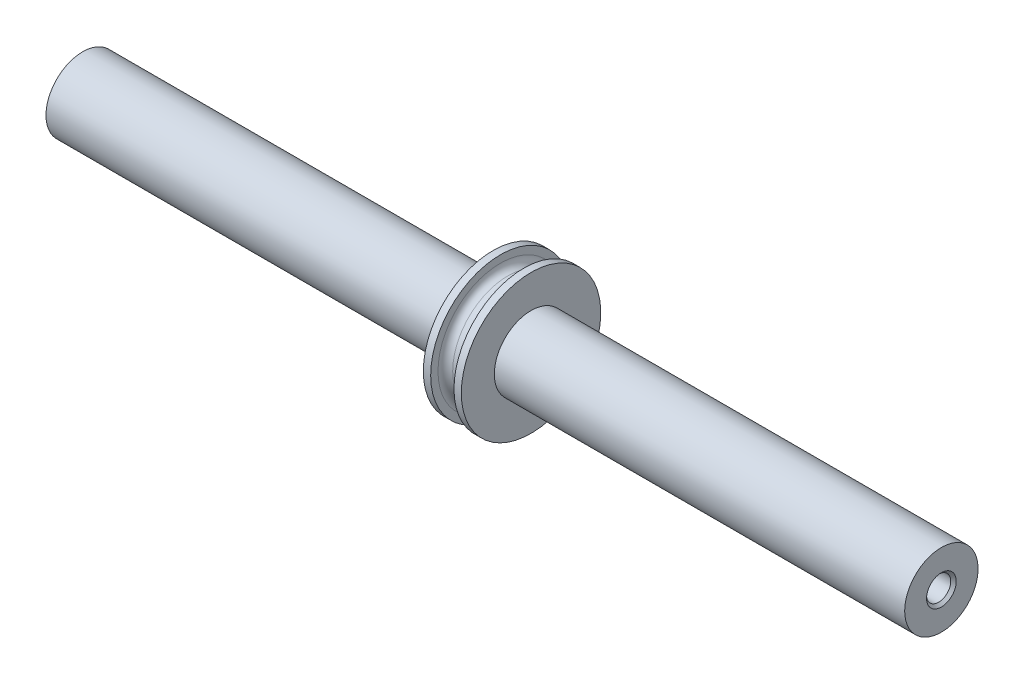
SolidWorks part; units mm, degrees
ref_plane "Front Plane" through (0, 0, 0) normal (0, 0, 1) x (1, 0, 0)
ref_plane "Top Plane" through (0, 0, 0) normal (0, 1, 0) x (1, 0, 0)
ref_plane "Right Plane" through (0, 0, 0) normal (1, 0, 0) x (0, 0, -1)
sketch "Sketch1" plane through (0, 0, 0) normal (0, 1, 0) x (1, 0, 0)
  line L0 (0, -55) -> (0, 55) construction
  line L1 (1.5875, 0) -> (-1.5875, 0)
  line L2 (0, 0) -> (0, 7.5)
  line L3 (1.5875, 7.5) -> (-1.5875, 7.5)
  line L4 (-1.5875, 0) -> (-1.5875, 7.5)
  line L5 (-1.5875, 0) -> (-2.5875, 0)
  line L6 (-1.5875, 0) -> (-1.5875, 9.5)
  line L7 (-1.5875, 9.5) -> (-2.5875, 9.5)
  line L8 (-2.5875, 0) -> (-2.5875, 9.5)
  line L9 (2.5875, 0) -> (2.5875, 9.5)
  line L10 (1.5875, 9.5) -> (2.5875, 9.5)
  line L11 (1.5875, 0) -> (1.5875, 9.5)
  line L12 (1.5875, 0) -> (2.5875, 0)
  line L13 (1.5875, 0) -> (1.5875, 7.5)
  line L14 (-2.6468, 0) -> (2.6468, 0) construction
  line L15 (2.5875, 0) -> (58.5, 0)
  line L16 (-2.5875, 0) -> (-58.5, 0)
  line L17 (-2.5875, 0) -> (-2.5875, 5)
  line L18 (-2.5875, 5) -> (-58.5, 5)
  line L19 (-58.5, 0) -> (-58.5, 5)
  line L20 (58.5, 0) -> (58.5, 5)
  line L21 (2.5875, 5) -> (58.5, 5)
  point P20 (0, 0)
  dimension "D1" = 7.5
  dimension "D2" = 1
  dimension "D3" = 1.5875
  dimension "D4" = 2
  dimension "D6" = 117
  dimension "D7" = 10
revolve "Revolve1" add sketch "Sketch1" angle 360 about L14
fillet "Fillet1" radius 1 2 edges at (-1.5875, 0, 7.5) (1.5875, 0, 7.5)
hole_wizard "M4x0.7 Tapped Hole1" positions "3DSketch2" profile "Sketch3" tap size "M4x0.7" standard "ANSI Metric"
sketch3d "3DSketch2"
  circle A0 centre (-58.5, 0, 0) radius 5 construction
  point P0 (-58.5, 0, 0)
  point P6 (-63.5, 0, 0)
sketch "Sketch3" plane through (-58.5, 0, 0) normal (0, 1, 0) x (0, 0, 1)
  line L0 (0, 0) -> (0, 15.9914)
  line L1 (0, 15.9914) -> (1.65, 15)
  line L2 (1.65, 15) -> (1.65, 0.375)
  line L3 (1.65, 0.375) -> (2.025, 0)
  line L5 (2.025, 0) -> (0, 0)
  line L6 (-1.65, 0.375) -> (-2.025, 0) construction
  line L10 (0, 15.9914) -> (-1.65, 15) construction
  line L11 (0, -6.35) -> (0, 107.95) construction
  dimension "Tap Drill Dia." = 3.3
  dimension "Tap Drill Depth" = 15
  dimension "Near C'Sink Dia." = 4.05
  dimension "Near C'Sink Angle" = 90
  dimension "Drill Angle" = 118
cosmetic thread "Hole Thread1" parameters "D1"=8, "D2"=4
mirror "Mirror1" about plane through (0, 0, 0) normal (1, 0, 0) of "M4x0.7 Tapped Hole1"
cosmetic thread "Hole Thread2" parameters "D1"=8, "D2"=4
